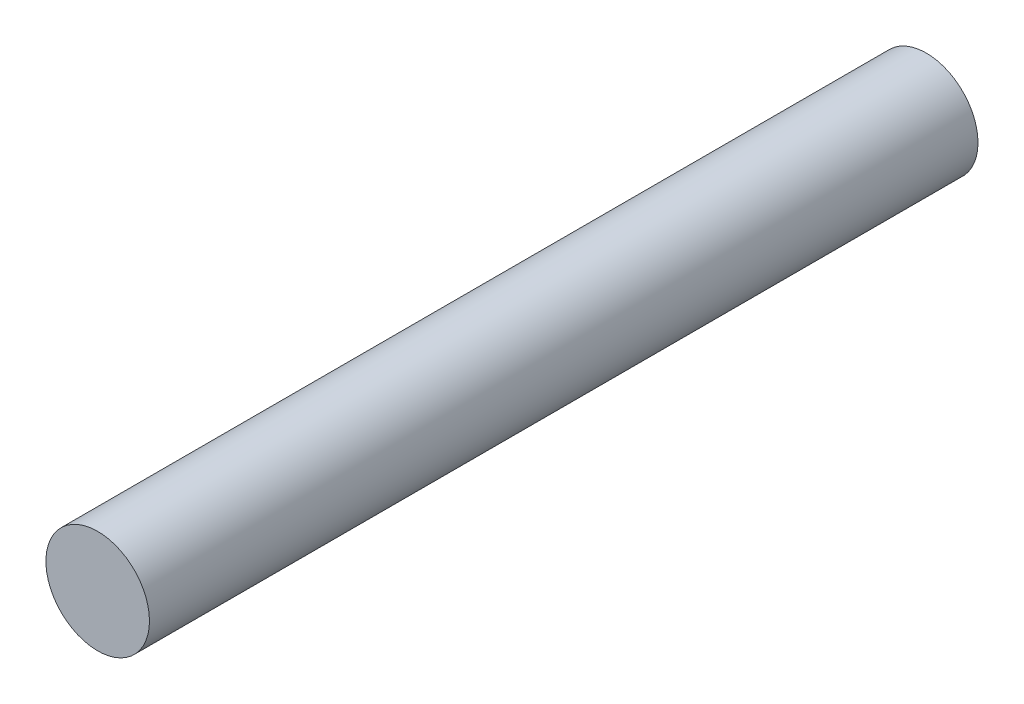
SolidWorks part; units mm, degrees
ref_plane "Front Plane" through (0, 0, 0) normal (0, 0, 1) x (1, 0, 0)
ref_plane "Top Plane" through (0, 0, 0) normal (0, 1, 0) x (1, 0, 0)
ref_plane "Right Plane" through (0, 0, 0) normal (1, 0, 0) x (0, 0, -1)
sketch "Sketch1" plane through (0, 0, 0) normal (0, 0, 1) x (1, 0, 0)
  circle A0 centre (0, 0) radius 2.5
extrude "Boss-Extrude1" add sketch "Sketch1" along normal blind 40
